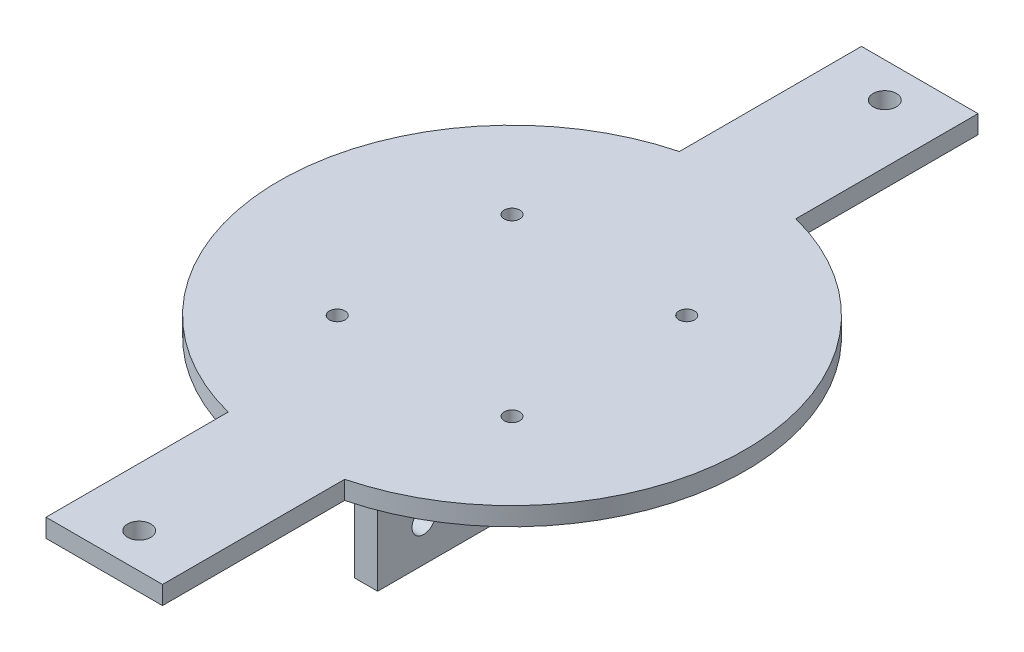
SolidWorks part; units mm, degrees
ref_plane "Front Plane" through (0, 0, 0) normal (0, 0, 1) x (1, 0, 0)
ref_plane "Top Plane" through (0, 0, 0) normal (0, 1, 0) x (1, 0, 0)
ref_plane "Right Plane" through (0, 0, 0) normal (1, 0, 0) x (0, 0, -1)
sketch "Sketch1" plane through (0, 0, 0) normal (0, 1, 0) x (1, 0, 0)
  line L0 (-12.7, 49.1869) -> (-12.7, 88.9)
  line L1 (12.7, -88.9) -> (-12.7, -88.9)
  line L2 (12.7, -88.9) -> (12.7, -49.1869)
  line L3 (12.7, 88.9) -> (-12.7, 88.9)
  line L4 (-12.7, -88.9) -> (-12.7, -49.1869)
  line L5 (12.7, -88.9) -> (-12.7, 88.9) construction
  line L6 (12.7, 88.9) -> (-12.7, -88.9) construction
  line L7 (12.7, 49.1869) -> (12.7, 88.9)
  arc A0 (-12.7, 49.1869) -> (-12.7, -49.1869) centre (0, 0) ccw
  arc A1 (12.7, -49.1869) -> (12.7, 49.1869) centre (0, 0) ccw
  dimension "D1" = 101.6
  dimension "D2" = 177.8
  dimension "D3" = 25.4
extrude "Boss-Extrude1" add sketch "Sketch1" along normal blind 4
sketch "Sketch3" plane through (0, 0, 0) normal (0, -1, 0) x (-1, 0, 0)
  line L1 (15.16, 44.45) -> (10.16, 44.45)
  line L2 (15.16, 44.45) -> (15.16, -44.45)
  line L3 (15.16, -44.45) -> (10.16, -44.45)
  line L4 (10.16, 44.45) -> (10.16, -44.45)
  line L5 (-10.16, -44.45) -> (-15.16, -44.45)
  line L6 (-10.16, -44.45) -> (-10.16, 44.45)
  line L7 (-10.16, 44.45) -> (-15.16, 44.45)
  line L8 (-15.16, -44.45) -> (-15.16, 44.45)
  point P8 (-12.66, -44.45)
  dimension "D1" = 20.32
  dimension "D2" = 10.16
  dimension "D3" = 5
  dimension "D4" = 5
  dimension "D5" = 44.45
  dimension "D6" = 44.45
  dimension "D7" = 88.9
  dimension "D8" = 88.9
extrude "Boss-Extrude2" add sketch "Sketch3" along normal blind 18.288
sketch "Sketch4" plane through (0, 4, 0) normal (0, 1, 0) x (1, 0, 0)
  line L1 (-19.05, 19.05) -> (19.05, 19.05) construction
  line L2 (-19.05, 19.05) -> (-19.05, -19.05) construction
  line L3 (-19.05, -19.05) -> (19.05, -19.05) construction
  line L4 (19.05, 19.05) -> (19.05, -19.05) construction
  line L5 (-19.05, 19.05) -> (19.05, -19.05) construction
  line L6 (-19.05, -19.05) -> (19.05, 19.05) construction
  point P0 (0, 0)
  point P1 (19.05, -19.05)
  point P2 (-19.05, 19.05)
  point P3 (-19.05, -19.05)
  point P4 (19.05, 19.05)
  point P15 (19.05, -19.05)
  point P17 (19.05, 19.05)
  point P19 (-19.05, 19.05)
  point P21 (-19.05, -19.05)
  dimension "D1" = 38.1
  dimension "D2" = 38.1
hole_wizard "M3 Clearance Hole1" positions "Sketch4" profile "Sketch5" hole size "M3" standard "ANSI Metric"
sketch "Sketch5" plane through (-19.05, 4, 19.05) normal (1, 0, 0) x (0, 0, 1)
  line L0 (0, 0) -> (0, 22.288)
  line L1 (0, 22.288) -> (1.7, 22.288)
  line L2 (1.7, 22.288) -> (1.7, 0)
  line L5 (1.7, 0) -> (0, 0)
  line L11 (0, -6.35) -> (0, 107.95) construction
  dimension "Thru Hole Dia." = 3.4
  dimension "Thru Hole Depth" = 22.288
fillet "Fillet1" radius 0.5 6 edges at (12.66, 0, 44.45) (15.16, 0, 0) (12.66, 0, -44.45) (-12.66, 0, -44.45) (-15.16, 0, 0) (-12.66, 0, 44.45)
sketch "Sketch6" plane through (-15.16, 0, 0) normal (-1, 0, 0) x (0, 0, 1)
  line L3 (-44.45, -18.288) -> (-44.45, -0.5) construction
  line L6 (44.45, -18.288) -> (44.45, -0.5) construction
  line L7 (-44.95, 0) -> (44.95, 0) construction
  circle A0 centre (34.417, -10.033) radius 2.54
  circle A1 centre (-34.417, -10.033) radius 2.54
  point P12 (0, 0)
  point P13 (0, 0)
  dimension "D1" = 5.08
  dimension "D2" = 5.08
  dimension "D4" = 10.033
  dimension "D5" = 10.033
  dimension "D3" = 10.033
extrude "Cut-Extrude1" cut sketch "Sketch6" against normal through all contours A0 | A1
sketch "Sketch7" plane through (0, 4, 0) normal (0, 1, 0) x (1, 0, 0)
  line L0 (12.7, 88.9) -> (-12.7, 88.9) construction
  line L1 (-12.7, 88.9) -> (-12.7, 49.1869) construction
  line L2 (-1.2906, 0) -> (-50.8, 0) construction
  line L4 (-12.7, -88.9) -> (12.7, -88.9) construction
  circle A0 centre (0, 81.28) radius 2.54
  circle A2 centre (0, -81.28) radius 2.54
  point P4 (0, 88.9)
  dimension "D1" = 5.08
  dimension "D2" = 7.62
  dimension "D3" = 12.7
  dimension "D4" = 7.62
extrude "Cut-Extrude2" cut sketch "Sketch7" against normal through all
